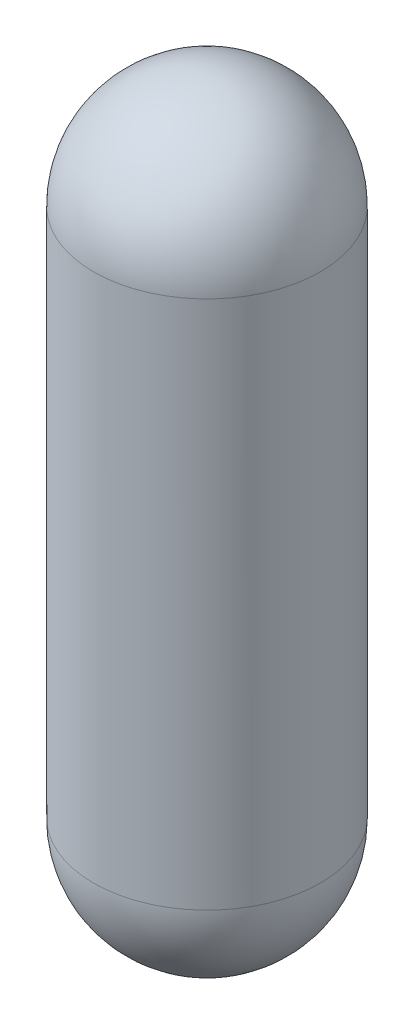
SolidWorks part; units mm, degrees
ref_plane "Front Plane" through (0, 0, 0) normal (0, 0, 1) x (1, 0, 0)
ref_plane "Top Plane" through (0, 0, 0) normal (0, 1, 0) x (1, 0, 0)
ref_plane "Right Plane" through (0, 0, 0) normal (1, 0, 0) x (0, 0, -1)
sketch "Sketch2" plane through (0, 0, 0) normal (0, 0, 1) x (1, 0, 0)
  line L0 (0, 17.5) -> (0, -17.5) construction
  line L4 (7.5, -17.5) -> (7.5, 17.5)
  line L5 (0, 25) -> (0, -25)
  arc A0 (0, 25) -> (7.5, 17.5) centre (0, 17.5) cw
  arc A1 (0, -25) -> (7.5, -17.5) centre (0, -17.5) ccw
  point P0 (0, 0)
  dimension "D2" = 7.5
  dimension "D1" = 35
revolve "Revolve6" add sketch "Sketch2" angle 360 about L0
